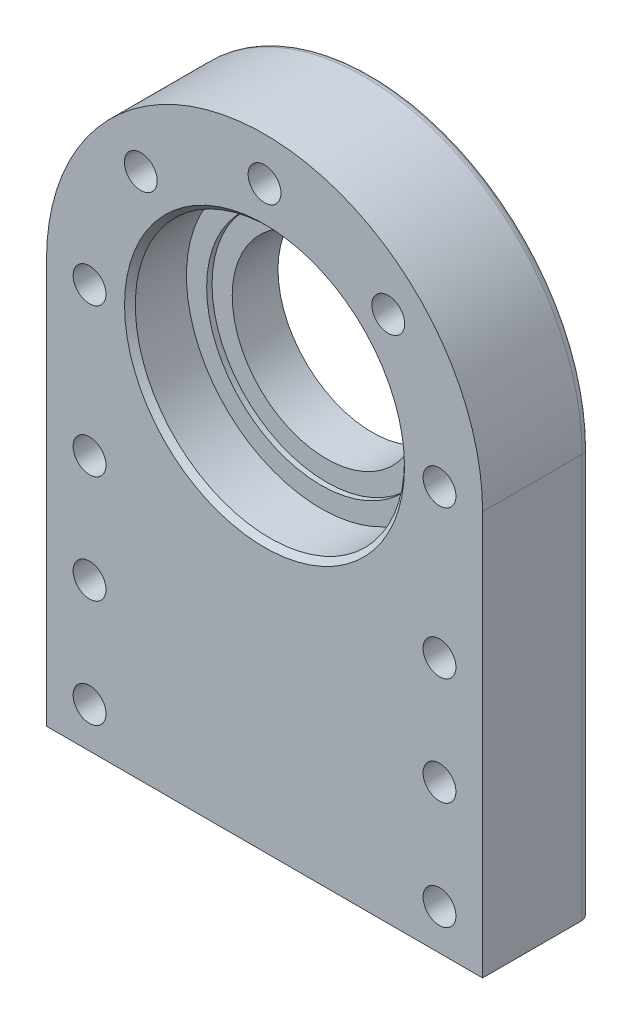
SolidWorks part; units mm, degrees
ref_plane "Front Plane" through (0, 0, 0) normal (0, 0, 1) x (1, 0, 0)
ref_plane "Top Plane" through (0, 0, 0) normal (0, 1, 0) x (1, 0, 0)
ref_plane "Right Plane" through (0, 0, 0) normal (1, 0, 0) x (0, 0, -1)
sketch "Sketch1" plane through (0, 0, 0) normal (0, 0, 1) x (1, 0, 0)
  line L0 (-81, 0) -> (-81, -150)
  line L1 (-81, -150) -> (81, -150)
  line L2 (81, -150) -> (81, 0)
  arc A0 (81, 0) -> (-81, 0) centre (0, 0) ccw
  dimension "D1" = 162
  dimension "D2" = 150
extrude "Boss-Extrude1" add sketch "Sketch1" along normal blind 40
sketch "Sketch2" plane through (0, 0, 40) normal (0, 0, 1) x (1, 0, 0)
  circle A0 centre (0, 0) radius 65 construction
  circle A1 centre (-65, 0) radius 6.1
  dimension "D1" = 130
  dimension "D2" = 12.2
extrude "Cut-Extrude1" cut sketch "Sketch2" against normal blind 40
pattern_circular "CirPattern1" count 5 over 180 about axis through (0, 0, 0) along (0, 0, 1) of "Cut-Extrude1"
sketch "Sketch3" plane through (0, 0, 40) normal (0, 0, 1) x (1, 0, 0)
  line L0 (-81, 0) -> (-81, -150) construction
  line L1 (-81, -150) -> (81, -150) construction
  circle A0 centre (-65, -135) radius 6.1
  circle A1 centre (-65, -95) radius 6.1
  circle A2 centre (-65, -55) radius 6.1
  point P6 (0, 0)
  point P7 (0, 0)
  point P8 (0, 0)
  dimension "D1" = 12.2
  dimension "D2" = 16
  dimension "D3" = 15
  dimension "D4" = 40
  dimension "D5" = 40
extrude "Cut-Extrude2" cut sketch "Sketch3" against normal blind 40
mirror "Mirror1" about plane through (0, 0, 0) normal (1, 0, 0) of "Cut-Extrude2"
sketch "Sketch4" plane through (0, 0, 40) normal (0, 0, 1) x (1, 0, 0)
  circle A0 centre (0, 0) radius 50
  dimension "D1" = 100
extrude "Cut-Extrude3" cut sketch "Sketch4" against normal blind 21
sketch "Sketch5" plane through (0, 0, 19) normal (0, 0, 1) x (1, 0, 0)
  circle A0 centre (0, 0) radius 42.5
  dimension "D1" = 85
extrude "Cut-Extrude4" cut sketch "Sketch5" against normal blind 2
sketch "Sketch6" plane through (0, 0, 17) normal (0, 0, 1) x (1, 0, 0)
  circle A0 centre (0, 0) radius 35
  dimension "D1" = 70
extrude "Cut-Extrude5" cut sketch "Sketch6" against normal blind 17
chamfer "Chamfer1" distance 2 1 edges at (50, 0, 40)
fillet "Fillet1" radius 3 4 edges at (0, -150, 0) (-81, -75, 0) (0, 81, 0) (81, -75, 0)
